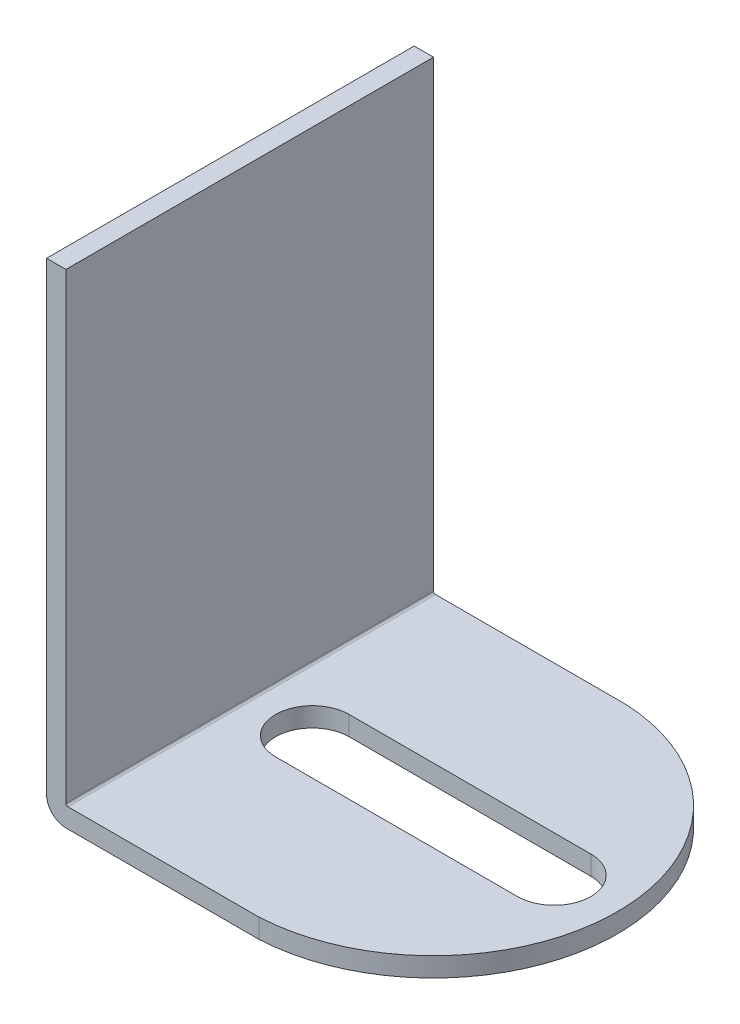
SolidWorks part; units mm, degrees
ref_plane "Front Plane" through (0, 0, 0) normal (0, 0, 1) x (1, 0, 0)
ref_plane "Top Plane" through (0, 0, 0) normal (0, 1, 0) x (1, 0, 0)
ref_plane "Right Plane" through (0, 0, 0) normal (1, 0, 0) x (0, 0, -1)
sketch "Sketch1" plane through (0, 0, 0) normal (0, 0, 1) x (1, 0, 0)
  line L0 (-20, 25) -> (-20, 23)
  line L1 (-18, 23) -> (-18, 25)
  line L2 (-18, 25) -> (-20, 25)
  line L3 (20, -23) -> (1, -23)
  line L4 (1, -25) -> (20, -25)
  line L5 (1, -25) -> (1, -23)
  line L6 (-18, -25) -> (1, -25)
  line L7 (1, -23) -> (-17.8, -23)
  line L8 (-18, -22.8) -> (-18, 23)
  line L9 (-20, 23) -> (-20, -23)
  line L10 (20, -25) -> (20, -23)
  arc A0 (-20, -23) -> (-18, -25) centre (-18, -23) ccw
  arc A1 (-18, -22.8) -> (-17.8, -23) centre (-17.8, -22.8) ccw
extrude "Boss-Extrude1" add sketch "Sketch1" along normal blind 38 contours A1 L8 L1 L2 L0 L9 A0 L6 L5 L7 | L4 L10 L3 L5
sketch "Sketch2" plane through (0, -25, 0) normal (0, -1, 0) x (1, 0, 0)
  line L0 (-18, 38) -> (20, 38) construction
  line L1 (0, 38) -> (20, 38)
  line L2 (20, 38) -> (20, 0)
  line L3 (20, 0) -> (0, 0)
  line L4 (-11.5206, 19) -> (13.4706, 19) construction
  line L5 (-11.5206, 22.8006) -> (13.4706, 22.8006)
  line L6 (-11.5206, 15.1994) -> (13.4706, 15.1994)
  arc A0 (0, 38) -> (0, 0) centre (0.975, 19) cw
  arc A1 (-11.5206, 22.8006) -> (-11.5206, 15.1994) centre (-11.5206, 19) ccw
  arc A2 (13.4706, 15.1994) -> (13.4706, 22.8006) centre (13.4706, 19) ccw
  point P12 (0.975, 19)
extrude "Cut-Extrude1" cut sketch "Sketch2" against normal blind 38
